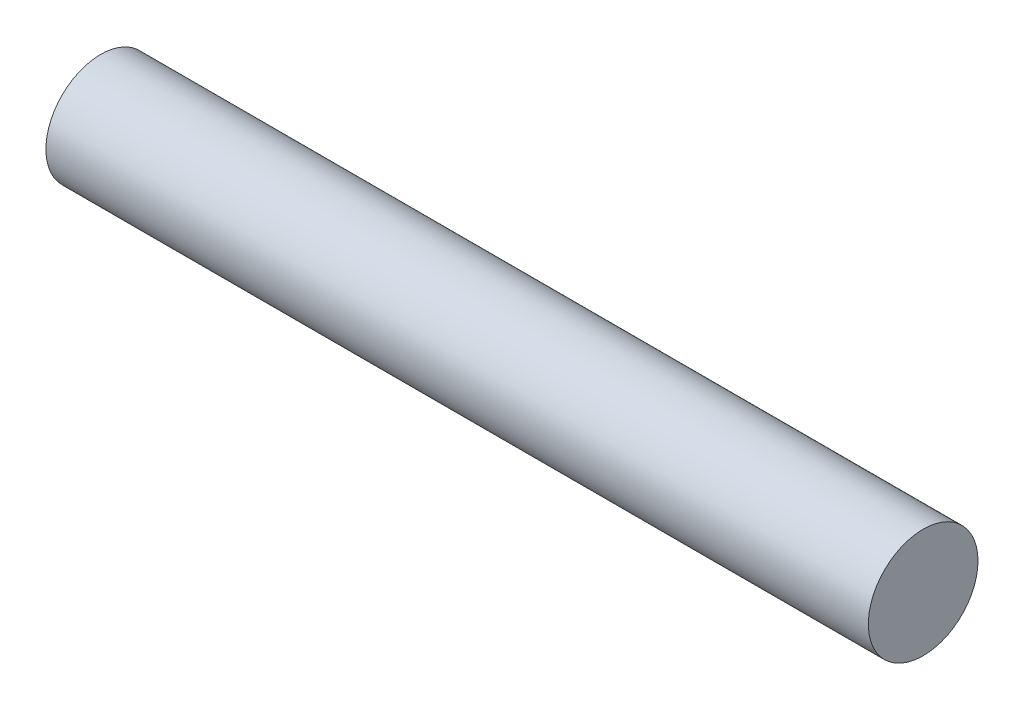
SolidWorks part; units mm, degrees
ref_plane "Front Plane" through (0, 0, 0) normal (0, 0, 1) x (1, 0, 0)
ref_plane "Top Plane" through (0, 0, 0) normal (0, 1, 0) x (1, 0, 0)
ref_plane "Right Plane" through (0, 0, 0) normal (1, 0, 0) x (0, 0, -1)
sketch "Sketch1" plane through (0, 0, 0) normal (1, 0, 0) x (0, 0, -1)
  circle A0 centre (0, 0) radius 1.27
  dimension "D1" = 2.54
extrude "Boss-Extrude1" add sketch "Sketch1" along normal blind 19.05
